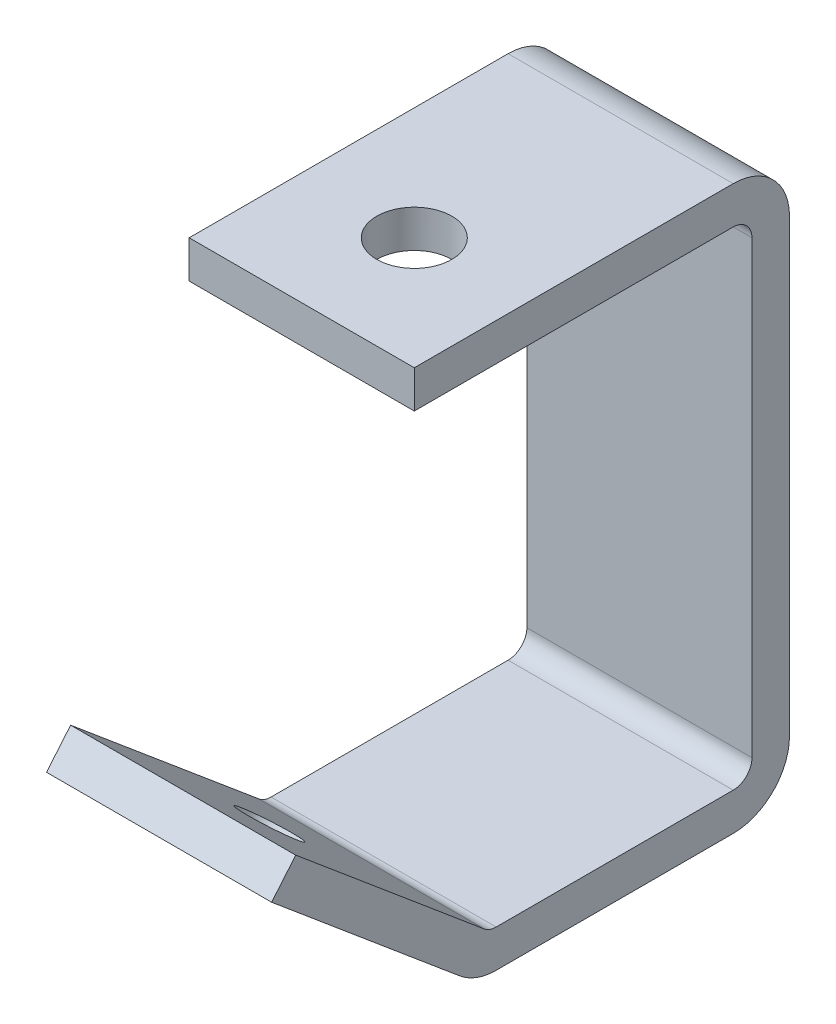
SolidWorks part; units mm, degrees
ref_plane "front" through (0, 0, 0) normal (0, 0, 1) x (1, 0, 0)
ref_plane "top" through (0, 0, 0) normal (0, 1, 0) x (1, 0, 0)
ref_plane "right" through (0, 0, 0) normal (1, 0, 0) x (0, 0, -1)
other "Configuration Table"
sketch "Sketch1" plane through (0, 0, 0) normal (1, 0, 0) x (0, 0, -1)
  line L0 (0, 0) -> (0, 82.55)
  line L1 (0, 82.55) -> (-57.15, 82.55)
  line L4 (-77.2165, 27.4943) -> (-44.45, 0)
  line L5 (-44.45, 0) -> (0, 0)
  dimension "D1" = 82.55
  dimension "D2" = 57.15
  dimension "D3" = 40
  dimension "D4" = 42.7736
  dimension "D5" = 44.45
extrude "Base-Extrude-Thin" add sketch "Sketch1" along normal mid plane 38.1 thin
sketch "Sketch2" plane through (0, 88.9, 0) normal (0, 1, 0) x (-1, 0, 0)
  line L0 (0, 50) -> (0, -50) construction
  line L1 (-19.05, 57.15) -> (19.05, 57.15) construction
  circle A0 centre (0, 38.1) radius 6.35
  dimension "D1" = 12.7
  dimension "D2" = 19.05
extrude "Cut-Extrude1" cut sketch "Sketch2" against normal up to next
sketch "Sketch3" plane through (0, -21.8874, 18.3657) normal (0, 0.766, -0.6428) x (1, 0, 0)
  circle A0 centre (0, -57.7582) radius 4.7625 construction
  circle A1 centre (0, -57.7582) radius 4.7625
extrude "Cut-Extrude2" cut sketch "Sketch3" against normal through all
